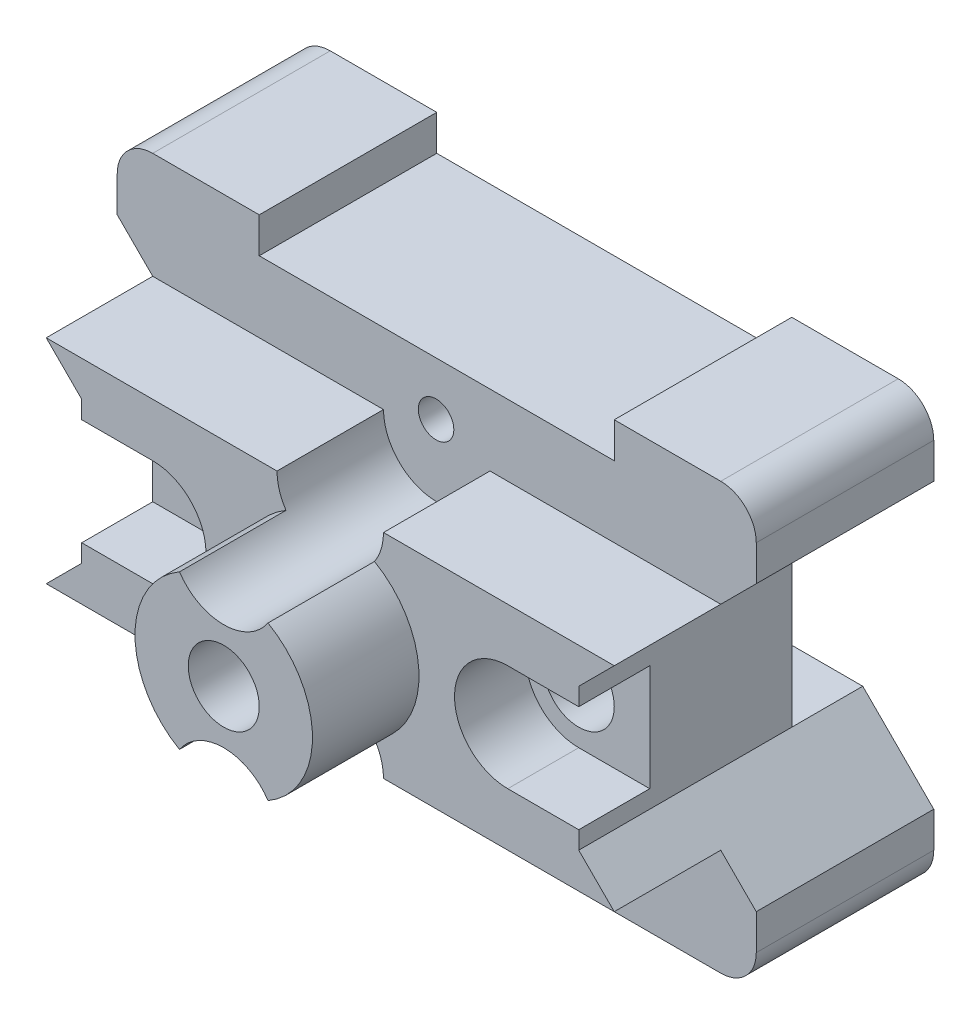
SolidWorks part; units mm, degrees
ref_plane "Front Plane" through (0, 0, 0) normal (0, 0, 1) x (1, 0, 0)
ref_plane "Top Plane" through (0, 0, 0) normal (0, 1, 0) x (1, 0, 0)
ref_plane "Right Plane" through (0, 0, 0) normal (1, 0, 0) x (0, 0, -1)
sketch "Sketch1" plane through (0, 0, 0) normal (0, 0, 1) x (1, 0, 0)
  line L0 (-90, 0) -> (-90, 5)
  line L1 (-85, 10) -> (-70, 10)
  line L2 (-70, 10) -> (-70, 5)
  line L3 (-70, 5) -> (-20, 5)
  line L4 (-20, 5) -> (-20, 10)
  line L5 (-20, 10) -> (-5, 10)
  line L6 (0, 5) -> (0, 0)
  line L7 (0, 0) -> (-10, -10)
  line L8 (-10, -10) -> (-10, -30)
  line L9 (-10, -30) -> (0, -40)
  line L10 (0, -40) -> (0, -45)
  line L11 (-5, -50) -> (-20, -50)
  line L12 (-20, -50) -> (-20, -45)
  line L13 (-20, -45) -> (-70, -45)
  line L14 (-70, -45) -> (-70, -50)
  line L15 (-90, -45) -> (-90, -40)
  line L16 (-85, -50) -> (-70, -50)
  line L17 (-90, -40) -> (-80, -30)
  line L18 (-80, -30) -> (-80, -10)
  line L19 (-80, -10) -> (-90, 0)
  arc A0 (-90, 5) -> (-85, 10) centre (-85, 5) cw
  arc A1 (-5, 10) -> (0, 5) centre (-5, 5) cw
  arc A2 (0, -45) -> (-5, -50) centre (-5, -45) cw
  arc A3 (-85, -50) -> (-90, -45) centre (-85, -45) cw
  dimension "D1" = 15
  dimension "D2" = 5
  dimension "D3" = 5
  dimension "D4" = 50
  dimension "D5" = 15
  dimension "D6" = 5
  dimension "D7" = 10
  dimension "D8" = 10
  dimension "D9" = 10
  dimension "D10" = 10
  dimension "D11" = 5
  dimension "D12" = 15
  dimension "D13" = 15
  dimension "D14" = 50
  dimension "D15" = 5
  dimension "D16" = 5
  dimension "D17" = 5
  dimension "D18" = 10
  dimension "D19" = 10
  dimension "D20" = 5
  dimension "D21" = 10
  dimension "D22" = 10
  dimension "D23" = 20
  dimension "D24" = 20
extrude "Boss-Extrude1" add sketch "Sketch1" along normal blind 60
sketch "Sketch2" plane through (0, 0, 0) normal (1, 0, 0) x (0, 0, -1)
  line L0 (-45, -40) -> (-15, -40)
  line L1 (-60, -40) -> (0, -40) construction
  line L2 (-15, -40) -> (-15, -50)
  line L3 (-15, -50) -> (-45, -50)
  line L4 (-45, -50) -> (-45, -40)
  dimension "D1" = 10
  dimension "D2" = 15
  dimension "D3" = 15
extrude "Cut-Extrude1" cut sketch "Sketch2" against normal blind 253
sketch "Sketch3" plane through (0, 0, 60) normal (0, 0, 1) x (1, 0, 0)
  line L0 (-85, -5) -> (-80, -10)
  line L1 (-90, 0) -> (-80, -10) construction
  line L2 (-80, -10) -> (-80, -30)
  line L3 (-80, -30) -> (-85, -35)
  line L4 (-80, -30) -> (-90, -40) construction
  line L5 (-85, -35) -> (-52.5, -35)
  line L6 (-37.5, -35) -> (-5, -35)
  line L7 (0, -40) -> (-10, -30) construction
  line L8 (-5, -35) -> (-10, -30)
  line L9 (-10, -30) -> (-10, -10)
  line L10 (-10, -10) -> (-5, -5)
  line L11 (-10, -10) -> (0, 0) construction
  line L12 (-85, -5) -> (-52.5, -5)
  line L13 (-37.5, -5) -> (-5, -5)
  arc A0 (-52.5, -35) -> (-37.5, -35) centre (-45, -35) cw
  arc A1 (-52.5, -5) -> (-37.5, -5) centre (-45, -5) ccw
  dimension "D1" = 7.5
  dimension "D2" = 7.5
extrude "Boss-Extrude2" add sketch "Sketch3" along normal blind 15
sketch "Sketch4" plane through (0, 0, 75) normal (0, 0, 1) x (1, 0, 0)
  line L0 (-80, -12.5) -> (-70, -12.5)
  line L1 (-80, -10) -> (-80, -30) construction
  line L2 (-70, -27.5) -> (-80, -27.5)
  line L3 (-80, -27.5) -> (-80, -12.5)
  line L4 (-10, -12.5) -> (-10, -27.5)
  line L5 (-10, -30) -> (-10, -10) construction
  line L6 (-10, -27.5) -> (-20, -27.5)
  line L7 (-20, -12.5) -> (-10, -12.5)
  arc A0 (-70, -12.5) -> (-70, -27.5) centre (-70, -20) cw
  arc A1 (-20, -27.5) -> (-20, -12.5) centre (-20, -20) cw
  dimension "D1" = 7.5
  dimension "D3" = 10
  dimension "D2" = 2.5
  dimension "D4" = 10
extrude "Cut-Extrude5" cut sketch "Sketch4" against normal blind 10
sketch "Sketch8" plane through (0, 0, 65) normal (0, 0, 1) x (1, 0, 0)
  circle A0 centre (-20, -20) radius 5
  circle A1 centre (-70, -20) radius 5
  dimension "D1" = 10
  dimension "D2" = 10
extrude "Cut-Extrude6" cut sketch "Sketch8" against normal blind 124
sketch "Sketch11" plane through (0, 0, 75) normal (0, 0, 1) x (1, 0, 0)
  line L0 (-70, -20) -> (-20, -20)
  line L1 (-45, -20) -> (-45, -21.7532)
  arc A0 (-51.2361, -9.1667) -> (-51.2361, -30.8333) centre (-45, -20) ccw
  arc A1 (-38.8396, -9.1234) -> (-51.2361, -9.1667) centre (-45.0523, -5.0134) cw
  arc A2 (-51.2361, -30.8333) -> (-38.7639, -30.8333) centre (-45, -35) cw
  arc A3 (-38.7639, -30.8333) -> (-38.8396, -9.1234) centre (-45, -20) ccw
  arc A5 (-52.5, -5) -> (-37.5, -5) centre (-45, -5) ccw construction
  arc A7 (-52.5, -5) -> (-37.5, -5) centre (-45, -5) ccw construction
  arc A8 (-37.5, -35) -> (-52.5, -35) centre (-45, -35) ccw construction
  point P0 (-45, -17.9534)
  point P3 (-52.0287, -7.6167)
  point P4 (-37.9713, -7.6167)
  point P8 (-40, -29.4098)
  point P12 (-50, -29.4098)
  dimension "D1" = 25
extrude "Boss-Extrude3" add sketch "Sketch11" along normal blind 15
sketch "Sketch15" plane through (-80, 0, 0) normal (-1, 0, 0) x (0, 0, 1)
  line L0 (45, -50) -> (45, 10)
  line L1 (45, 10) -> (0, 10)
  line L3 (45, -50) -> (0, -50)
  line L4 (0, 10) -> (0, -50)
extrude "Cut-Extrude8" cut sketch "Sketch15" against normal mid plane 180
sketch "Sketch16" plane through (0, 0, 45) normal (0, 0, -1) x (-1, 0, 0)
  line L0 (10, -10) -> (80, -10)
  line L1 (80, -30) -> (10, -30)
  line L20 (90, -45) -> (90, -40)
  line L21 (90, -40) -> (80, -30)
  line L22 (80, -30) -> (80, -10)
  line L23 (80, -10) -> (90, 0)
  line L24 (90, 0) -> (90, 5)
  line L25 (85, 10) -> (70, 10)
  line L26 (70, 10) -> (70, 5)
  line L27 (70, 5) -> (20, 5)
  line L28 (20, 5) -> (20, 10)
  line L29 (20, 10) -> (5, 10)
  line L30 (0, 5) -> (0, 0)
  line L31 (0, 0) -> (10, -10)
  line L32 (10, -10) -> (10, -30)
  line L33 (10, -30) -> (0, -40)
  line L34 (0, -40) -> (0, -45)
  line L35 (5, -50) -> (20, -50)
  line L36 (20, -50) -> (20, -45)
  line L37 (20, -45) -> (70, -45)
  line L38 (70, -45) -> (70, -50)
  line L39 (70, -50) -> (85, -50)
  line L40 (90, -45) -> (90, -40)
  line L41 (90, -40) -> (80, -30)
  line L43 (80, -10) -> (90, 0)
  line L44 (90, 0) -> (90, 5)
  line L45 (85, 10) -> (70, 10)
  line L46 (70, 10) -> (70, 5)
  line L47 (70, 5) -> (20, 5)
  line L48 (20, 5) -> (20, 10)
  line L49 (20, 10) -> (5, 10)
  line L50 (0, 5) -> (0, 0)
  line L51 (0, 0) -> (10, -10)
  line L53 (10, -30) -> (0, -40)
  line L54 (0, -40) -> (0, -45)
  line L55 (5, -50) -> (20, -50)
  line L56 (20, -50) -> (20, -45)
  line L57 (20, -45) -> (70, -45)
  line L58 (70, -45) -> (70, -50)
  line L59 (70, -50) -> (85, -50)
  arc A4 (90, 5) -> (85, 10) centre (85, 5) ccw
  arc A5 (5, 10) -> (0, 5) centre (5, 5) ccw
  arc A6 (0, -45) -> (5, -50) centre (5, -45) ccw
  arc A7 (85, -50) -> (90, -45) centre (85, -45) ccw
  arc A8 (90, 5) -> (85, 10) centre (85, 5) ccw
  arc A9 (5, 10) -> (0, 5) centre (5, 5) ccw
  arc A10 (0, -45) -> (5, -50) centre (5, -45) ccw
  arc A11 (85, -50) -> (90, -45) centre (85, -45) ccw
  dimension "D1" = 0
extrude "Boss-Extrude4" add sketch "Sketch16" along normal blind 10
sketch "Sketch21" plane through (0, 0, 60) normal (0, 0, 1) x (1, 0, 0)
  point P0 (-45.0961, -37.4982)
  point P4 (-45.0961, -2.5018)
  point P8 (0, 0)
hole_wizard "Ø1.2 (1.2) Diameter Hole7" positions "3DSketch3" profile "Sketch22" hole size "Ø1.2" standard "ISO"
sketch3d "3DSketch3"
  point P0 (-45.0961, -2.5018, 60)
  point P3 (-45.0961, -37.4982, 60)
sketch "Sketch22" plane through (-45.0961, -2.5018, 60) normal (1, 0, 0) x (0, -1, 0)
  line L0 (0, 0) -> (0, 11.3574)
  line L1 (0, 11.3574) -> (2.5, 10)
  line L2 (2.5, 10) -> (2.5, 0)
  line L5 (2.5, 0) -> (0, 0)
  line L10 (0, 11.3574) -> (-2.5, 10) construction
  line L11 (0, -6.35) -> (0, 107.95) construction
  dimension "Hole Dia." = 5
  dimension "Hole Depth" = 10
  dimension "Drill Angle" = 123
hole_wizard "Ø10.0 (10) Diameter Hole4" positions "3DSketch7" profile "Sketch26" hole size "Ø10.0" standard "ISO"
sketch3d "3DSketch7"
  line L0 (-45, -20, 90) -> (-45, -20, 75) construction
  point P0 (-45, -20, 90)
sketch "Sketch26" plane through (-45, -20, 90) normal (1, 0, 0) x (0, -1, 0)
  line L0 (0, 0) -> (0, 22.7148)
  line L1 (0, 22.7148) -> (5, 20)
  line L2 (5, 20) -> (5, 0)
  line L5 (5, 0) -> (0, 0)
  line L10 (0, 22.7148) -> (-5, 20) construction
  line L11 (0, -6.35) -> (0, 107.95) construction
  dimension "Hole Dia." = 10
  dimension "Hole Depth" = 20
  dimension "Drill Angle" = 123
